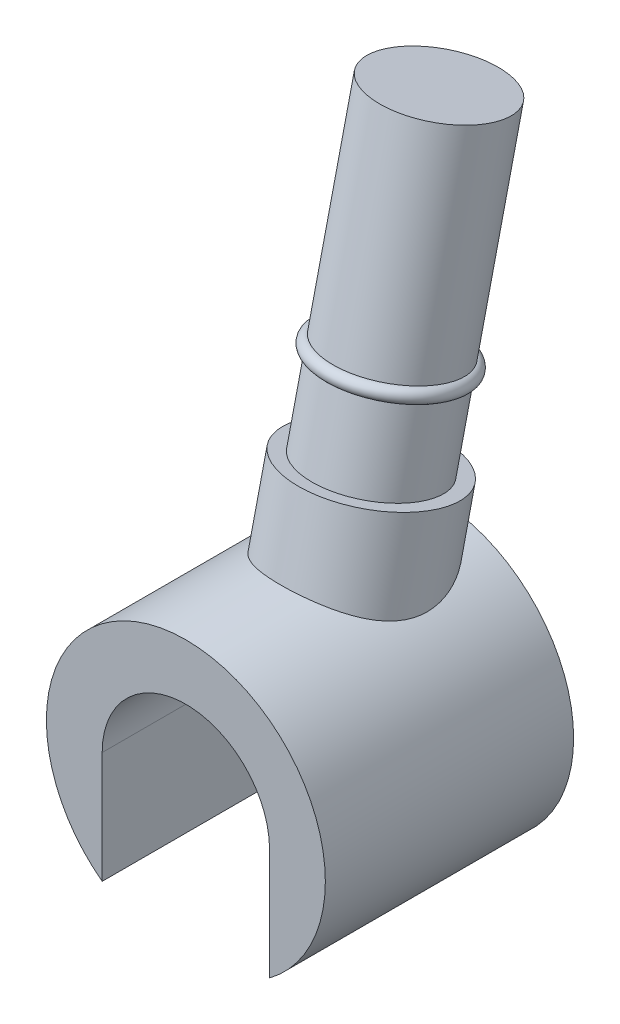
SolidWorks part; units mm, degrees
ref_plane "Front Plane" through (0, 0, 0) normal (0, 0, 1) x (1, 0, 0)
ref_plane "Top Plane" through (0, 0, 0) normal (0, 1, 0) x (1, 0, 0)
ref_plane "Right Plane" through (0, 0, 0) normal (1, 0, 0) x (0, 0, -1)
sketch "Sketch1" plane through (0, 0, 0) normal (0, 0, 1) x (1, 0, 0)
  line L0 (-1.5, 0) -> (-1.5, -2)
  line L1 (1.5, 0) -> (1.5, -2)
  arc A0 (1.5, 0) -> (-1.5, 0) centre (0, 0) ccw
  arc A1 (1.5, -2) -> (-1.5, -2) centre (0, 0) ccw
  dimension "D1" = 3
  dimension "D2" = 5
extrude "Boss-Extrude1" add sketch "Sketch1" along normal blind 4.45
sketch "Sketch3" plane through (0, 0, 0) normal (1, 0, 0) x (0, 0, -1)
  line L0 (0, 8.5181) -> (0, -4.8787) construction
  line L1 (-5.3899, 2.5) -> (3.753, 2.5) construction
  line L2 (-2.8474, 9.984) -> (-2.8474, -4.178) construction
  line L3 (-0.628, 12.113) -> (-2.8474, 2.5) construction
  line L4 (-2.8474, 2.5) -> (-3.8315, -1.7626) construction
  line L5 (0, 2.5) -> (0.1779, 3.2704)
  line L6 (0.1779, 3.2704) -> (-0.0657, 3.3267)
  line L7 (-0.0657, 3.3267) -> (0.2548, 4.7151)
  line L8 (1.149, 8.5883) -> (0.0872, 8.8334)
  line L9 (0.0872, 8.8334) -> (-1.4966, 1.9731)
  line L10 (-1.4966, 1.9731) -> (-0.1912, 1.6718)
  line L11 (-0.1912, 1.6718) -> (0, 2.5)
  line L12 (0.3111, 4.9587) -> (1.149, 8.5883)
  arc A0 (0.2548, 4.7151) -> (0.3111, 4.9587) centre (0.2829, 4.8369) ccw
  point P20 (-1.375, 2.5)
  dimension "D2" = 0.25
  dimension "D1" = 77
  dimension "D3" = 6.5
  dimension "D4" = 3.85
  dimension "D5" = 1.375
  dimension "D6" = 0.25
  dimension "D7" = 5.4
revolve "Revolve3" add sketch "Sketch3" angle 360 about L9
